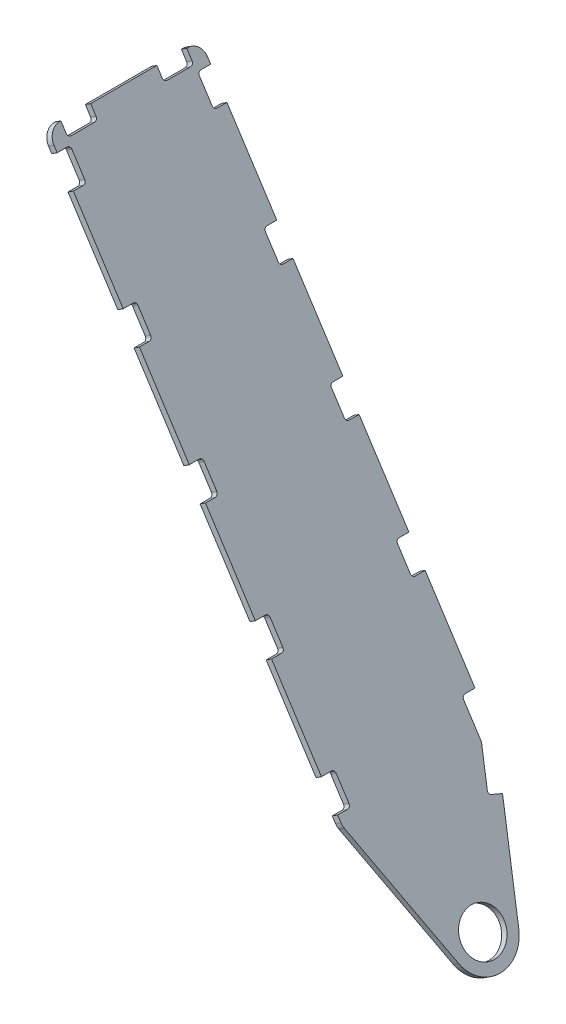
SolidWorks part; units mm, degrees
ref_plane "Front Plane" through (0, 0, 0) normal (0, 0, 1) x (1, 0, 0)
ref_plane "Top Plane" through (0, 0, 0) normal (0, 1, 0) x (1, 0, 0)
ref_plane "Right Plane" through (0, 0, 0) normal (1, 0, 0) x (0, 0, -1)
ref_plane "Plane4" through (106.6039, 69.014, 0) normal (0.8394, 0.5434, 0) x (-0.5434, 0.8394, 0)
sketch "Sketch1" plane through (106.6039, 69.014, 0) normal (0.8394, 0.5434, 0) x (-0.5434, 0.8394, 0)
  line L25 (2433.7569, -117.1428) -> (2433.7569, -136.7008)
  line L26 (2433.7569, -136.7008) -> (2445.4409, -136.7008)
  line L27 (2470.8409, -111.3008) -> (2470.8409, -109.1418)
  line L28 (2470.8409, -109.1418) -> (2451.2829, -109.1418)
  line L29 (2444.9329, -102.7918) -> (2444.9329, -56.3098)
  line L30 (2451.2829, -49.9598) -> (2470.8409, -49.9598)
  line L31 (2470.8409, -49.9598) -> (2470.8409, 81.3582)
  line L32 (2470.8409, 81.3582) -> (2451.2829, 81.3582)
  line L33 (2444.9329, 87.7082) -> (2444.9329, 134.1902)
  line L34 (2451.2829, 140.5402) -> (2470.8409, 140.5402)
  line L35 (2470.8409, 140.5402) -> (2470.8409, 142.6992)
  line L36 (2445.4409, 168.0992) -> (2433.7569, 168.0992)
  line L37 (2433.7569, 168.0992) -> (2433.7569, 148.5412)
  line L38 (2427.4069, 142.1912) -> (2380.9249, 142.1912)
  line L39 (2374.5749, 148.5412) -> (2374.5749, 168.0992)
  line L40 (2374.5749, 168.0992) -> (2192.4569, 168.0992)
  line L41 (2192.4569, 168.0992) -> (2192.4569, 148.5412)
  line L42 (2186.1069, 142.1912) -> (2139.6249, 142.1912)
  line L43 (2133.2749, 148.5412) -> (2133.2749, 168.0992)
  line L44 (2133.2749, 168.0992) -> (1951.1569, 168.0992)
  line L45 (1951.1569, 168.0992) -> (1951.1569, 148.5412)
  line L46 (1944.8069, 142.1912) -> (1898.3249, 142.1912)
  line L47 (1891.9749, 148.5412) -> (1891.9749, 168.0992)
  line L48 (1891.9749, 168.0992) -> (1709.8569, 168.0992)
  line L49 (1709.8569, 168.0992) -> (1709.8569, 148.5412)
  line L50 (1703.5069, 142.1912) -> (1657.0249, 142.1912)
  line L51 (1650.6749, 148.5412) -> (1650.6749, 168.0992)
  line L52 (1650.6749, 168.0992) -> (1468.5569, 168.0992)
  line L53 (1468.5569, 168.0992) -> (1468.5569, 148.5412)
  line L54 (1462.2069, 142.1912) -> (1415.7249, 142.1912)
  line L55 (1409.3749, 148.5412) -> (1409.3749, 168.0992)
  line L56 (1409.3749, 168.0992) -> (1397.0986, 168.0992)
  line L57 (1388.4113, 166.5674) -> (1137.8476, 75.3697)
  line L58 (1137.8476, -43.9712) -> (1317.7529, -109.4514)
  line L59 (1317.7529, -109.4514) -> (1324.4422, -91.0729)
  line L60 (1332.581, -87.2777) -> (1396.136, -110.4098)
  line L61 (1398.3078, -110.7928) -> (1462.2069, -110.7928)
  line L62 (1468.5569, -117.1428) -> (1468.5569, -136.7008)
  line L63 (1468.5569, -136.7008) -> (1650.6749, -136.7008)
  line L64 (1650.6749, -136.7008) -> (1650.6749, -117.1428)
  line L65 (1657.0249, -110.7928) -> (1703.5069, -110.7928)
  line L66 (1709.8569, -117.1428) -> (1709.8569, -136.7008)
  line L67 (1709.8569, -136.7008) -> (1891.9749, -136.7008)
  line L68 (1891.9749, -136.7008) -> (1891.9749, -117.1428)
  line L69 (1898.3249, -110.7928) -> (1944.8069, -110.7928)
  line L70 (1951.1569, -117.1428) -> (1951.1569, -136.7008)
  line L71 (1951.1569, -136.7008) -> (2133.2749, -136.7008)
  line L72 (2133.2749, -136.7008) -> (2133.2749, -117.1428)
  line L73 (2139.6249, -110.7928) -> (2186.1069, -110.7928)
  line L74 (2192.4569, -117.1428) -> (2192.4569, -136.7008)
  line L75 (2192.4569, -136.7008) -> (2374.5749, -136.7008)
  line L76 (2374.5749, -136.7008) -> (2374.5749, -117.1428)
  line L77 (2380.9249, -110.7928) -> (2427.4069, -110.7928)
  circle A25 centre (1159.5659, 15.6992) radius 42.291
  arc A26 (2445.4409, -136.7008) -> (2470.8409, -111.3008) centre (2445.4409, -111.3008) ccw
  arc A27 (2451.2829, -109.1418) -> (2444.9329, -102.7918) centre (2451.2829, -102.7918) cw
  arc A28 (2444.9329, -56.3098) -> (2451.2829, -49.9598) centre (2451.2829, -56.3098) cw
  arc A29 (2451.2829, 81.3582) -> (2444.9329, 87.7082) centre (2451.2829, 87.7082) cw
  arc A30 (2444.9329, 134.1902) -> (2451.2829, 140.5402) centre (2451.2829, 134.1902) cw
  arc A31 (2470.8409, 142.6992) -> (2445.4409, 168.0992) centre (2445.4409, 142.6992) ccw
  arc A32 (2433.7569, 148.5412) -> (2427.4069, 142.1912) centre (2427.4069, 148.5412) cw
  arc A33 (2380.9249, 142.1912) -> (2374.5749, 148.5412) centre (2380.9249, 148.5412) cw
  arc A34 (2192.4569, 148.5412) -> (2186.1069, 142.1912) centre (2186.1069, 148.5412) cw
  arc A35 (2139.6249, 142.1912) -> (2133.2749, 148.5412) centre (2139.6249, 148.5412) cw
  arc A36 (1951.1569, 148.5412) -> (1944.8069, 142.1912) centre (1944.8069, 148.5412) cw
  arc A37 (1898.3249, 142.1912) -> (1891.9749, 148.5412) centre (1898.3249, 148.5412) cw
  arc A38 (1709.8569, 148.5412) -> (1703.5069, 142.1912) centre (1703.5069, 148.5412) cw
  arc A39 (1657.0249, 142.1912) -> (1650.6749, 148.5412) centre (1657.0249, 148.5412) cw
  arc A40 (1468.5569, 148.5412) -> (1462.2069, 142.1912) centre (1462.2069, 148.5412) cw
  arc A41 (1415.7249, 142.1912) -> (1409.3749, 148.5412) centre (1415.7249, 148.5412) cw
  arc A42 (1397.0986, 168.0992) -> (1388.4113, 166.5674) centre (1397.0986, 142.6992) ccw
  arc A43 (1137.8476, 75.3697) -> (1137.8476, -43.9712) centre (1159.5659, 15.6992) ccw
  arc A44 (1324.4422, -91.0729) -> (1332.581, -87.2777) centre (1330.4092, -93.2448) cw
  arc A45 (1396.136, -110.4098) -> (1398.3078, -110.7928) centre (1398.3078, -104.4428) ccw
  arc A46 (1462.2069, -110.7928) -> (1468.5569, -117.1428) centre (1462.2069, -117.1428) cw
  arc A47 (1650.6749, -117.1428) -> (1657.0249, -110.7928) centre (1657.0249, -117.1428) cw
  arc A48 (1703.5069, -110.7928) -> (1709.8569, -117.1428) centre (1703.5069, -117.1428) cw
  arc A49 (1891.9749, -117.1428) -> (1898.3249, -110.7928) centre (1898.3249, -117.1428) cw
  arc A50 (1944.8069, -110.7928) -> (1951.1569, -117.1428) centre (1944.8069, -117.1428) cw
  arc A51 (2133.2749, -117.1428) -> (2139.6249, -110.7928) centre (2139.6249, -117.1428) cw
  arc A52 (2186.1069, -110.7928) -> (2192.4569, -117.1428) centre (2186.1069, -117.1428) cw
  arc A53 (2374.5749, -117.1428) -> (2380.9249, -110.7928) centre (2380.9249, -117.1428) cw
  arc A54 (2427.4069, -110.7928) -> (2433.7569, -117.1428) centre (2427.4069, -117.1428) cw
extrude "Boss-Extrude1" add sketch "Sketch1" against normal blind 12.7
